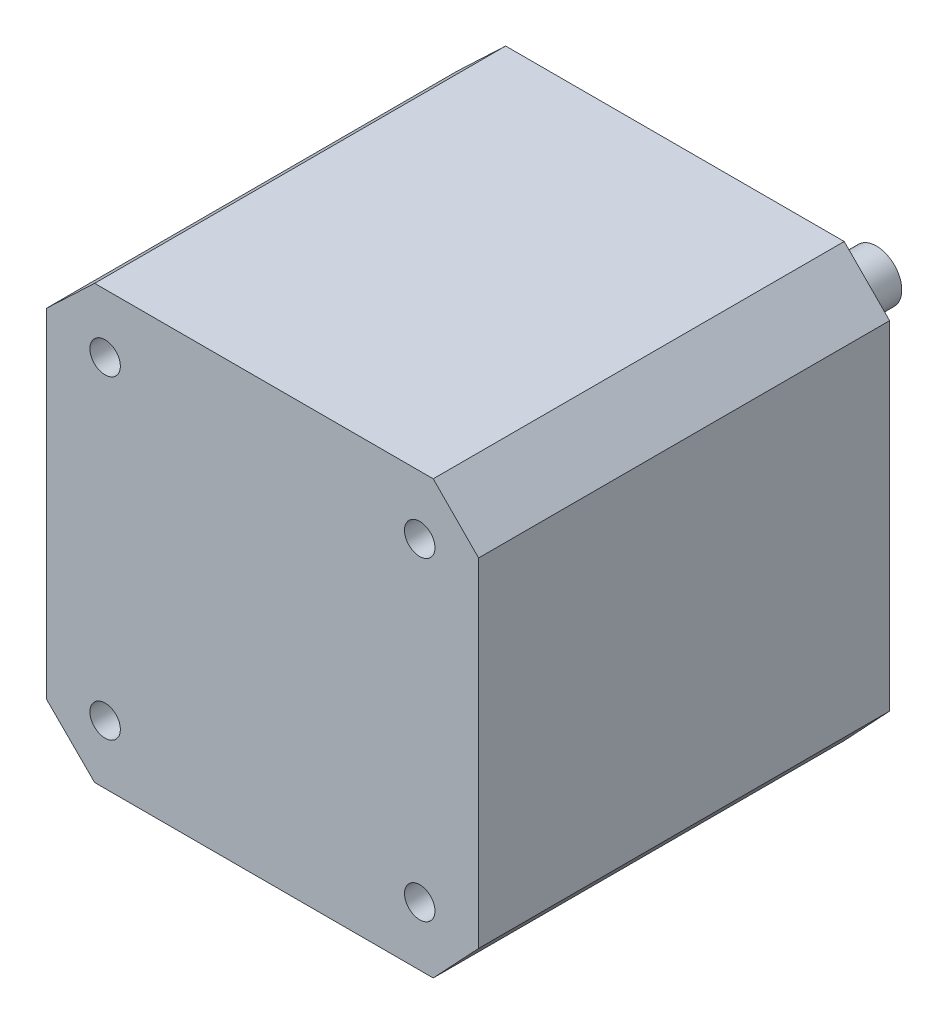
SolidWorks part; units mm, degrees
material "6063-T4"
ref_plane "Front Plane" through (0, 0, 0) normal (0, 0, 1) x (1, 0, 0)
ref_plane "Top Plane" through (0, 0, 0) normal (0, 1, 0) x (1, 0, 0)
ref_plane "Right Plane" through (0, 0, 0) normal (1, 0, 0) x (0, 0, -1)
sketch "Sketch1" plane through (0, 0, 0) normal (0, 0, 1) x (1, 0, 0)
  line L0 (0, -25.4) -> (42.6, -25.4)
  line L1 (0, -25.4) -> (0, 17.2)
  line L2 (0, 17.2) -> (42.6, 17.2)
  line L3 (42.6, 17.2) -> (42.6, -25.4)
  line L4 (56.702, -4.1) -> (-12.676, -4.1) construction
  line L5 (21.3, -28.067) -> (21.3, 19.2088) construction
  circle A0 centre (5.8, 11.4) radius 1.5
  circle A1 centre (5.8, -19.6) radius 1.5
  circle A2 centre (36.8, -19.6) radius 1.5
  circle A3 centre (36.8, 11.4) radius 1.5
  point P2 (21.3, -4.1)
  point P6 (5.8, 11.4)
  point P7 (36.8, 11.4)
  point P8 (36.8, -19.6)
  point P9 (5.8, -19.6)
  dimension "D1" = 42.6
  dimension "D2" = 42.6
  dimension "D3" = 21.3
  dimension "D4" = 21.3
  dimension "D5" = 15.5
  dimension "D6" = 15.5
  dimension "D7" = 31
  dimension "D8" = 31
extrude "Extrude1" add sketch "Sketch1" along normal blind 40.5
sketch "Sketch2" plane through (0, 0, 0) normal (0, 0, -1) x (-1, 0, 0)
  line L0 (-4.7644, -25.4) -> (0, -20.64)
  line L1 (0, -25.4) -> (-42.6, -25.4) construction
  line L2 (0, 17.2) -> (0, -25.4) construction
  line L3 (-4.7644, 17.2) -> (0, 12.6802)
  line L4 (-42.6, 17.2) -> (0, 17.2) construction
  line L5 (-38.1282, 17.2) -> (-42.6, 12.6802)
  line L6 (-42.6, -25.4) -> (-42.6, 17.2) construction
  line L7 (-42.6, 12.6802) -> (-42.6, 17.2)
  line L8 (-42.6, 17.2) -> (-38.1282, 17.2)
  line L9 (-38.1282, -25.4) -> (-42.6, -20.64)
  line L10 (-42.6, -20.64) -> (-42.6, -25.4)
  line L11 (-42.6, -25.4) -> (-38.1282, -25.4)
  line L12 (-4.7644, -25.4) -> (0, -25.4)
  line L13 (0, -25.4) -> (0, -20.64)
  line L14 (0, 12.6802) -> (0, 17.2)
  line L15 (0, 17.2) -> (-4.7644, 17.2)
extrude "Extrude2" cut sketch "Sketch2" against normal blind 40.5
sketch "Sketch5" plane through (0, 0, 0) normal (0, 0, -1) x (-1, 0, 0)
  line L0 (-36.8, -19.6) -> (-5.8, 11.4) construction
  line L1 (-5.8, -19.6) -> (-36.8, 11.4) construction
  circle A0 centre (-21.3, -4.1) radius 11
extrude "Extrude3" add sketch "Sketch5" along normal blind 2
sketch "Sketch6" plane through (0, 0, -2) normal (0, 0, -1) x (-1, 0, 0)
  line L0 (-5.8, 11.4) -> (-36.8, -19.6) construction
  line L1 (-5.8, -19.6) -> (-36.8, 11.4) construction
  circle A0 centre (-21.3, -4.1) radius 2.5
extrude "Extrude4" add sketch "Sketch6" along normal blind 18
